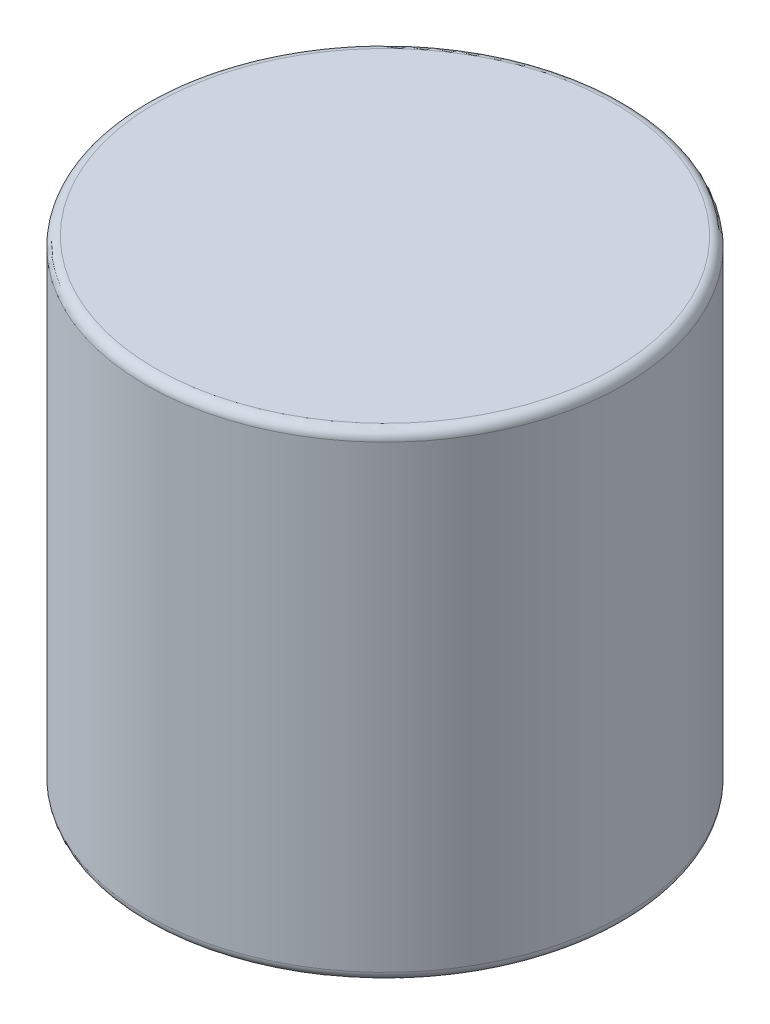
SolidWorks part; units mm, degrees
ref_plane "Front Plane" through (0, 0, 0) normal (0, 0, 1) x (1, 0, 0)
ref_plane "Top Plane" through (0, 0, 0) normal (0, 1, 0) x (1, 0, 0)
ref_plane "Right Plane" through (0, 0, 0) normal (1, 0, 0) x (0, 0, -1)
sketch "Sketch1" plane through (0, 0, 0) normal (0, 1, 0) x (1, 0, 0)
  circle A2 centre (0, 0) radius 5
  dimension "D1" = 10
extrude "Boss-Extrude1" add sketch "Sketch1" along normal blind 10
fillet "Fillet1" radius 0.2 2 edges at (0, 0, 5) (0, 10, 5)
